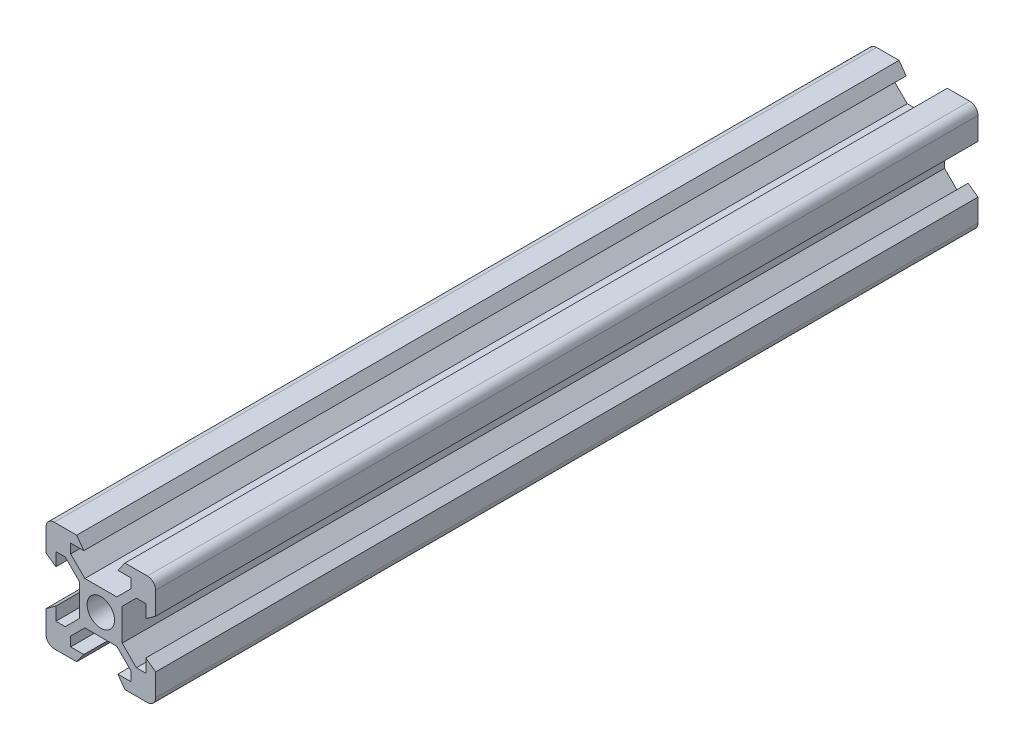
SolidWorks part; units mm, degrees
ref_plane "前视基准面" through (0, 0, 0) normal (0, 0, 1) x (1, 0, 0)
ref_plane "上视基准面" through (0, 0, 0) normal (0, 1, 0) x (1, 0, 0)
ref_plane "右视基准面" through (0, 0, 0) normal (1, 0, 0) x (0, 0, -1)
sketch "草图1" plane through (0, 0, 0) normal (0, 0, 1) x (1, 0, 0)
  line L0 (16.8101, 19.3214) -> (19.4, 21.9114) construction
  line L1 (14.8, 34.8214) -> (18.9, 34.8214)
  line L2 (13.3, 33.3214) -> (13.3, 29.2214)
  line L3 (14.8, 14.8214) -> (18.9, 14.8214)
  line L4 (33.3, 33.3214) -> (33.3, 29.2214)
  line L7 (27.2, 27.7315) -> (29.7899, 30.3214) construction
  line L8 (33.3, 29.2214) -> (31.5, 27.9214)
  line L9 (28.8, 31.3114) -> (26.2101, 28.7214)
  line L10 (31.5, 30.3214) -> (31.5, 27.9214)
  line L11 (29.7899, 30.3214) -> (31.5, 30.3214)
  line L12 (26.2101, 28.7214) -> (28.8, 31.3114) construction
  line L13 (27.2, 27.7315) -> (29.7899, 30.3214)
  line L15 (20.3899, 28.7214) -> (26.2101, 28.7214) construction
  line L18 (18.9, 34.8214) -> (20.2, 33.0214)
  line L19 (27.7, 34.8214) -> (26.4, 33.0214)
  line L20 (26.4, 33.0214) -> (28.8, 33.0214)
  line L21 (28.8, 33.0214) -> (28.8, 31.3114)
  line L22 (26.2101, 28.7214) -> (20.3899, 28.7214)
  line L25 (20.3899, 28.7214) -> (17.8, 31.3114)
  line L26 (17.8, 31.3114) -> (17.8, 33.0214)
  line L27 (17.8, 33.0214) -> (20.2, 33.0214)
  line L28 (27.2, 21.9114) -> (27.2, 27.7315)
  line L29 (29.7899, 19.3214) -> (27.2, 21.9114)
  line L30 (31.5, 19.3214) -> (29.7899, 19.3214)
  line L31 (31.5, 21.7214) -> (31.5, 19.3214)
  line L32 (33.3, 20.4214) -> (31.5, 21.7214)
  line L33 (27.7, 14.8214) -> (26.4, 16.6214)
  line L34 (28.8, 16.6214) -> (26.4, 16.6214)
  line L35 (28.8, 18.3315) -> (28.8, 16.6214)
  line L36 (26.2101, 20.9214) -> (28.8, 18.3315)
  line L37 (20.3899, 20.9214) -> (26.2101, 20.9214)
  line L38 (17.8, 18.3315) -> (20.3899, 20.9214)
  line L39 (17.8, 16.6214) -> (17.8, 18.3315)
  line L40 (20.2, 16.6214) -> (17.8, 16.6214)
  line L41 (18.9, 14.8214) -> (20.2, 16.6214)
  line L42 (13.3, 20.4214) -> (15.1, 21.7214)
  line L43 (15.1, 19.3214) -> (15.1, 21.7214)
  line L44 (16.8101, 19.3214) -> (15.1, 19.3214)
  line L45 (19.4, 21.9114) -> (16.8101, 19.3214)
  line L46 (19.4, 27.7315) -> (19.4, 21.9114)
  line L47 (16.8101, 30.3214) -> (19.4, 27.7315)
  line L48 (15.1, 30.3214) -> (16.8101, 30.3214)
  line L49 (15.1, 27.9214) -> (15.1, 30.3214)
  line L50 (13.3, 29.2214) -> (15.1, 27.9214)
  line L51 (27.7, 34.8214) -> (31.8, 34.8214)
  line L52 (33.3, 20.4214) -> (33.3, 16.3214)
  line L53 (13.3, 20.4214) -> (13.3, 16.3214)
  line L54 (27.7, 14.8214) -> (31.8, 14.8214)
  circle A0 centre (23.3, 24.8214) radius 2.5
  arc A1 (14.8, 34.8214) -> (13.3, 33.3214) centre (14.8, 33.3214) ccw
  arc A2 (33.3, 33.3214) -> (31.8, 34.8214) centre (31.8, 33.3214) ccw
  arc A3 (31.8, 14.8214) -> (33.3, 16.3214) centre (31.8, 16.3214) ccw
  arc A4 (14.8, 14.8214) -> (13.3, 16.3214) centre (14.8, 16.3214) cw
  point P11 (33.3, 34.8214)
  point P18 (33.3, 14.8214)
  dimension "D3" = 5
  dimension "D1" = 1.5
  dimension "D4" = 1.5
  dimension "D5" = 1.5
  dimension "D7" = 1.5
  dimension "D2" = 20
  dimension "D6" = 4
extrude "凸台-拉伸1" add sketch "草图1" along normal blind 150
